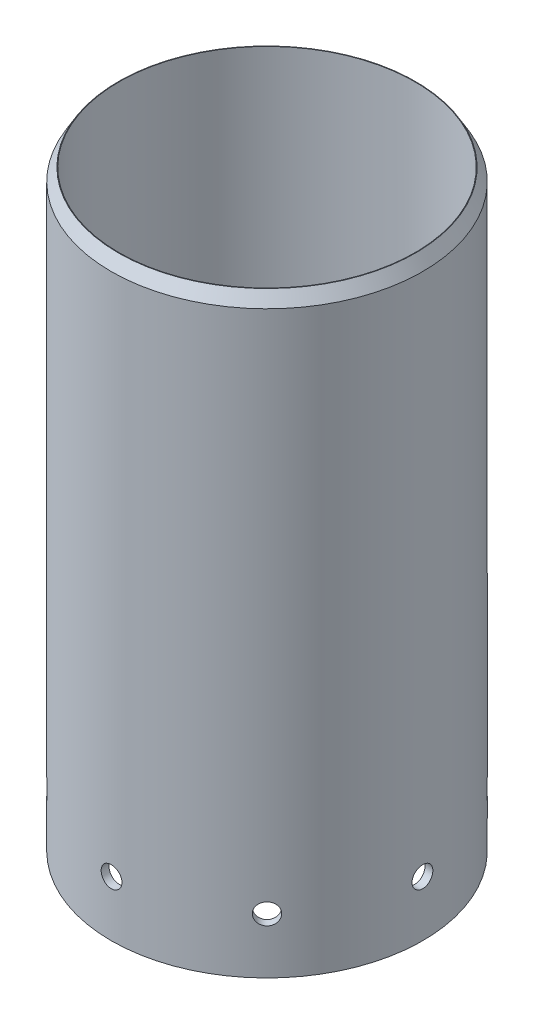
SolidWorks part; units mm, degrees
ref_plane "Front Plane" through (0, 0, 0) normal (0, 0, 1) x (1, 0, 0)
ref_plane "Top Plane" through (0, 0, 0) normal (0, 1, 0) x (1, 0, 0)
ref_plane "Right Plane" through (0, 0, 0) normal (1, 0, 0) x (0, 0, -1)
sketch "Sketch1" plane through (0, 0, 0) normal (0, 1, 0) x (1, 0, 0)
  circle A0 centre (0, 0) radius 106.934
  circle A1 centre (0, 0) radius 101.6
  dimension "D1" = 203.2
  dimension "D2" = 213.868
extrude "Boss-Extrude1" add sketch "Sketch1" along normal blind 406.4
chamfer "Chamfer2" distance 8.5514 distance2 4.9371 1 edges at (0, 406.4, 106.934)
sketch "Sketch3" plane through (0, 0, 0) normal (0, 1, 0) x (1, 0, 0)
  line L0 (0, 0) -> (106.934, 0) construction
  line L1 (106.934, 0) -> (98.7941, -40.9219) construction
  line L2 (98.7941, -40.9219) -> (0, 0) construction
  circle A0 centre (0, 0) radius 106.934 construction
  dimension "D1" = 22.5
ref_plane "Plane1" through (106.934, 0, 0) normal (1, 0, 0) x (0, 0, -1)
sketch "Sketch6" plane through (106.934, 0, 0) normal (1, 0, 0) x (0, 0, -1)
  line L0 (0, 0) -> (0, 38.1) construction
  circle A0 centre (0, 38.1) radius 7.1438
  dimension "D1" = 14.2875
  dimension "D2" = 38.1
extrude "Cut-Extrude1" cut sketch "Sketch6" along normal up to surface (5.5855 mm away)
pattern_circular "CirPattern1" count 8 over 360 about axis through (0, 406.4, 0) along (0, -1, 0) of "Cut-Extrude1"
equation "\"Top Taper\"= 4in"
